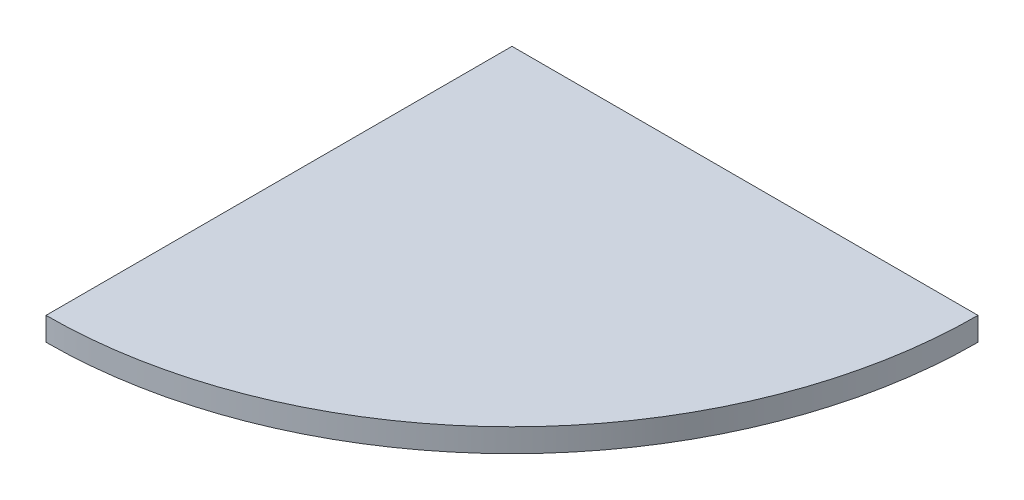
SolidWorks part; units mm, degrees
ref_plane "Front Plane" through (0, 0, 0) normal (0, 0, 1) x (1, 0, 0)
ref_plane "Top Plane" through (0, 0, 0) normal (0, 1, 0) x (1, 0, 0)
ref_plane "Right Plane" through (0, 0, 0) normal (1, 0, 0) x (0, 0, -1)
sketch "Sketch1" plane through (0, 0, 0) normal (0, 1, 0) x (1, 0, 0)
  line L0 (0, 0) -> (609.6, 0)
  line L1 (0, 0) -> (0, -609.6)
  arc A0 (0, -609.6) -> (609.6, 0) centre (0, 0) ccw
  dimension "D1" = 1219.2
extrude "Boss-Extrude1" add sketch "Sketch1" along normal mid plane 30.48
